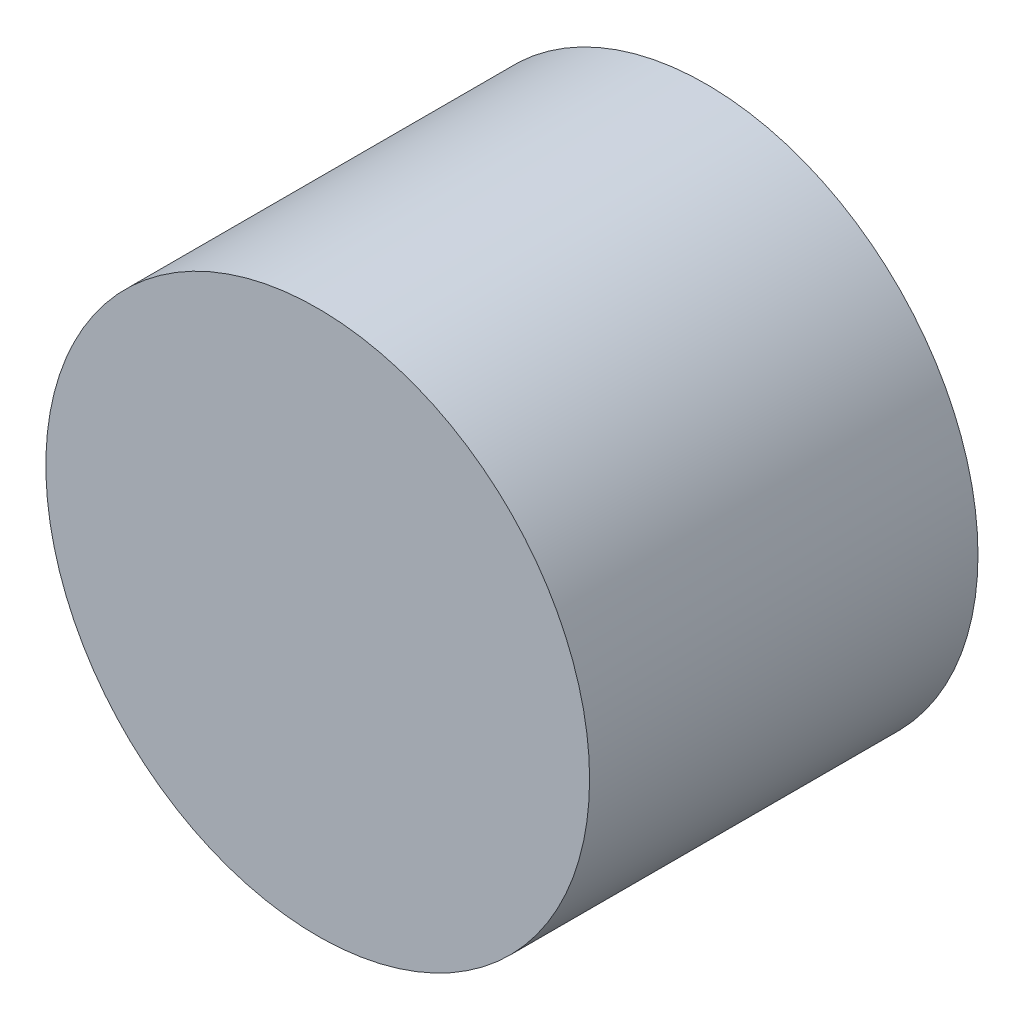
SolidWorks part; units mm, degrees
ref_plane "Front Plane" through (0, 0, 0) normal (1, 0, 0) x (0, 1, 0)
ref_plane "Top Plane" through (0, 0, 0) normal (0, 0, 1) x (0, 1, 0)
ref_plane "Right Plane" through (0, 0, 0) normal (0, 1, 0) x (-1, 0, 0)
sketch "Sketch1" plane through (0, 0, 0) normal (0, 0, 1) x (0, 1, 0)
  circle A0 centre (0, 0.3512) radius 35.56
  dimension "D1" = 71.12
extrude "Boss-Extrude1" add sketch "Sketch1" along normal blind 50.8
